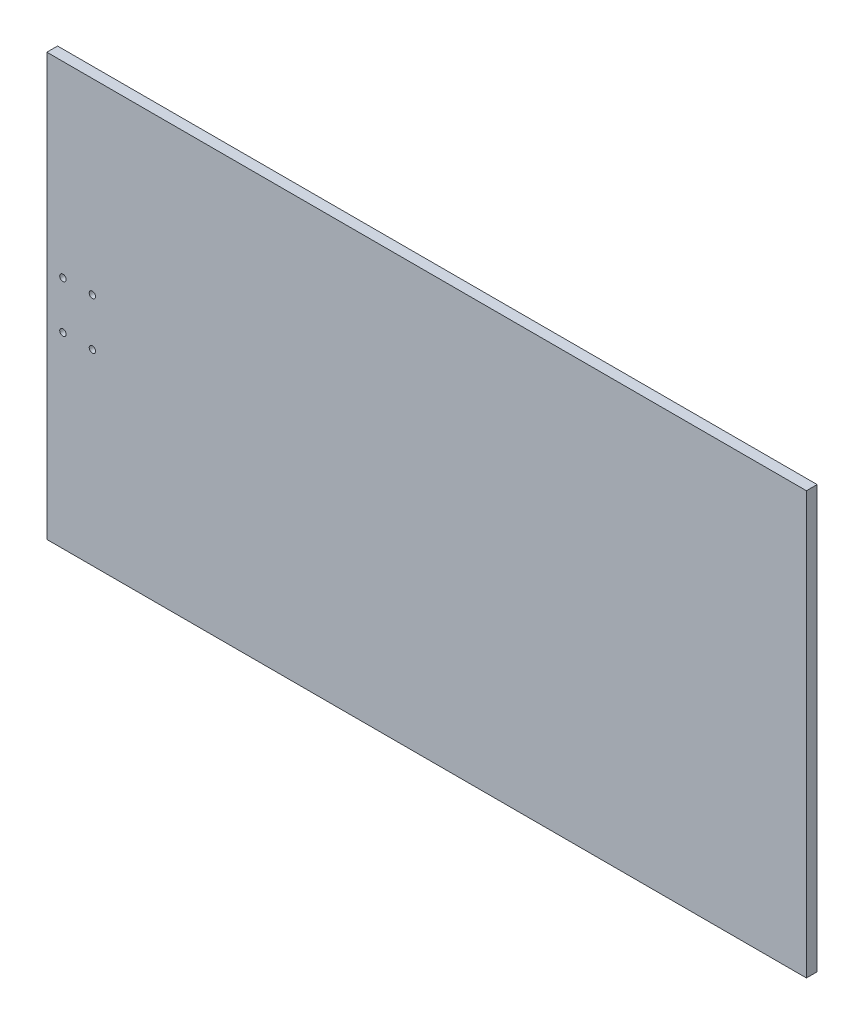
SolidWorks part; units mm, degrees
material "Balsa"
ref_plane "Front Plane" through (0, 0, 0) normal (0, 0, 1) x (1, 0, 0)
ref_plane "Top Plane" through (0, 0, 0) normal (0, 1, 0) x (1, 0, 0)
ref_plane "Right Plane" through (0, 0, 0) normal (1, 0, 0) x (0, 0, -1)
sketch "Sketch1" plane through (0, 0, 0) normal (0, 0, 1) x (1, 0, 0)
  line L1 (-225, -125) -> (225, -125)
  line L2 (-225, -125) -> (-225, 125)
  line L3 (-225, 125) -> (225, 125)
  line L4 (225, -125) -> (225, 125)
  line L5 (-225, -125) -> (225, 125) construction
  line L6 (-225, 125) -> (225, -125) construction
  point P0 (0, 0)
  dimension "D1" = 450
  dimension "D2" = 250
extrude "Boss-Extrude1" add sketch "Sketch1" along normal blind 6.35
sketch "Sketch2" plane through (0, 0, 6.35) normal (0, 0, 1) x (1, 0, 0)
  line L0 (-225, 0) -> (225, 0) construction
  line L1 (-225, 125) -> (-225, -125) construction
  line L2 (225, -125) -> (225, 125) construction
  point P6 (-199.6, 50.8)
  point P7 (-199.6, -50.8)
  dimension "D1" = 50.8
  dimension "D2" = 25.4
hole_wizard "1/4 Clearance Hole1" [suppressed] positions "Sketch3" profile "Sketch4" hole size "1/4" standard "ANSI Inch"
sketch "Sketch3" plane through (0, 0, 6.35) normal (0, 0, 1) x (1, 0, 0)
  point P0 (-199.6, 50.8)
  point P3 (-199.6, -50.8)
sketch "Sketch4" plane through (-199.6, 50.8, 6.35) normal (1, 0, 0) x (0, -1, 0)
  line L0 (0, 0) -> (0, 6.35)
  line L1 (0, 6.35) -> (3.3782, 6.35)
  line L2 (3.3782, 6.35) -> (3.3782, 0)
  line L5 (3.3782, 0) -> (0, 0)
  line L11 (0, -6.35) -> (0, 107.95) construction
  dimension "Thru Hole Dia." = 6.7564
  dimension "Thru Hole Depth" = 6.35
sketch "Sketch5" [suppressed] plane through (0, 0, 0) normal (0, 0, -1) x (-1, 0, 0)
  point P0 (-213.6335, -69.85)
  point P1 (-213.6335, -6.35)
  point P3 (-213.6335, 57.15)
hole_wizard "#6 Clearance Hole1" [suppressed] positions "Sketch6" profile "Sketch7" hole size "#6" standard "ANSI Inch"
sketch "Sketch6" [suppressed] plane through (0, 0, 6.35) normal (0, 0, 1) x (1, 0, 0)
  point P0 (213.6335, 57.15)
  point P3 (213.6335, -6.35)
  point P6 (213.6335, -69.85)
sketch "Sketch7" plane through (213.6335, 57.15, 6.35) normal (1, 0, 0) x (0, -1, 0)
  line L0 (0, 0) -> (0, 6.35)
  line L1 (0, 6.35) -> (1.8986, 6.35)
  line L2 (1.8986, 6.35) -> (1.8986, 0)
  line L5 (1.8986, 0) -> (0, 0)
  line L11 (0, -6.35) -> (0, 107.95) construction
  dimension "Thru Hole Dia." = 3.7973
  dimension "Thru Hole Depth" = 6.35
sketch "Sketch8" plane through (0, 0, 0) normal (0, 0, -1) x (-1, 0, 0)
  point P0 (215.475, -14)
  point P1 (198.0125, -14)
  point P3 (198.0125, 14)
  point P5 (215.475, 14)
hole_wizard "#6 Clearance Hole2" positions "Sketch9" profile "Sketch10" hole size "#6" standard "ANSI Inch" end condition through all
sketch "Sketch9" plane through (0, 0, 0) normal (0, 0, -1) x (-1, 0, 0)
  point P0 (198.0125, 14)
  point P3 (215.475, 14)
  point P6 (198.0125, -14)
  point P9 (215.475, -14)
sketch "Sketch10" plane through (-198.0125, 14, 0) normal (1, 0, 0) x (0, 1, 0)
  line L0 (0, 0) -> (0, 6.35)
  line L1 (0, 6.35) -> (1.8986, 6.35)
  line L2 (1.8986, 6.35) -> (1.8986, 0)
  line L5 (1.8986, 0) -> (0, 0)
  line L11 (0, -6.35) -> (0, 107.95) construction
  dimension "Thru Hole Dia." = 3.7973
  dimension "Thru Hole Depth" = 6.35
